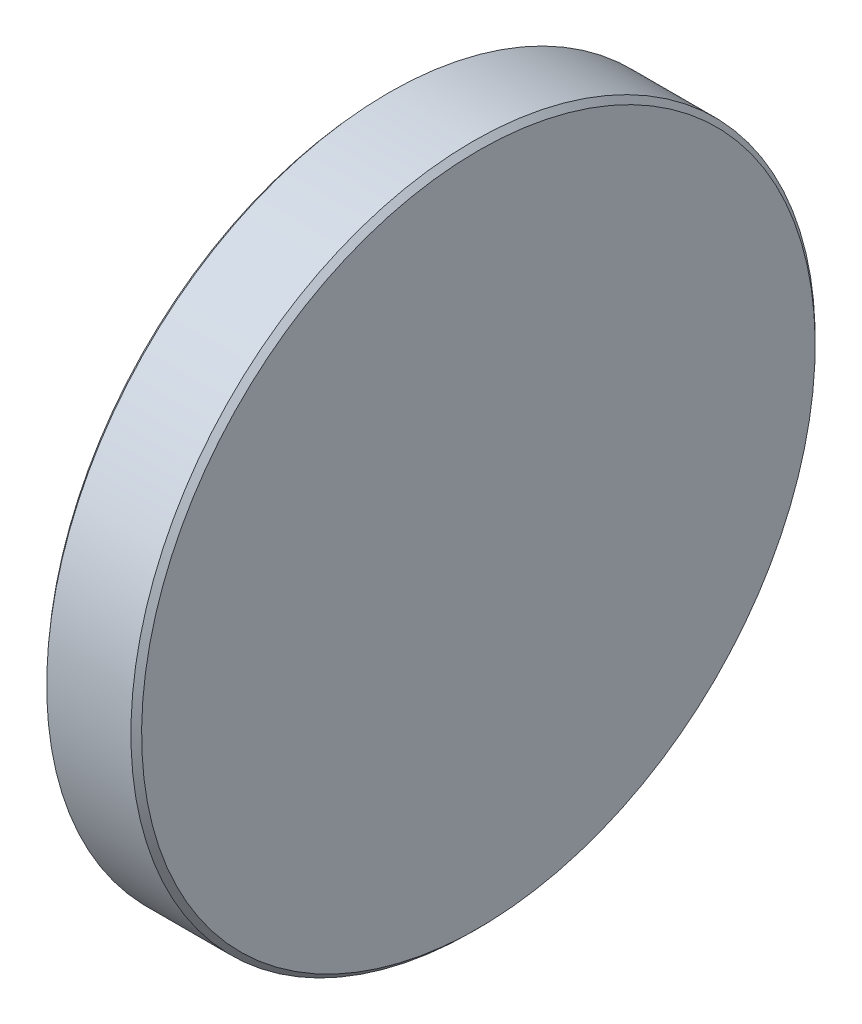
SolidWorks part; units mm, degrees
material "Стекло"
ref_plane "Front" through (0, 0, 0) normal (0, 0, 1) x (1, 0, 0)
ref_plane "Top" through (0, 0, 0) normal (0, 1, 0) x (1, 0, 0)
ref_plane "Right" through (0, 0, 0) normal (1, 0, 0) x (0, 0, -1)
sketch "Эскиз1" plane through (0, 0, 0) normal (0, 0, 1) x (1, 0, 0)
  line L0 (0, 0) -> (0, 16) construction
  line L1 (-0.4263, 16) -> (4, 16)
  line L2 (4, 16) -> (4, 0)
  line L3 (4, 0) -> (0, 0)
  line L4 (4, 0) -> (-2.3336, 0) construction
  arc A0 (0, 0) -> (-0.4263, 16) centre (-300.5, 0) ccw
  dimension "D3" = 300.5
  dimension "D1" = 32
  dimension "D2" = 4
revolve "Повернуть1" add sketch "Эскиз1" angle 360 about L4
chamfer "Фаска1" distance 0.25 angle 45 2 edges at (4, 16, 0) (-0.4263, 16, 0)
